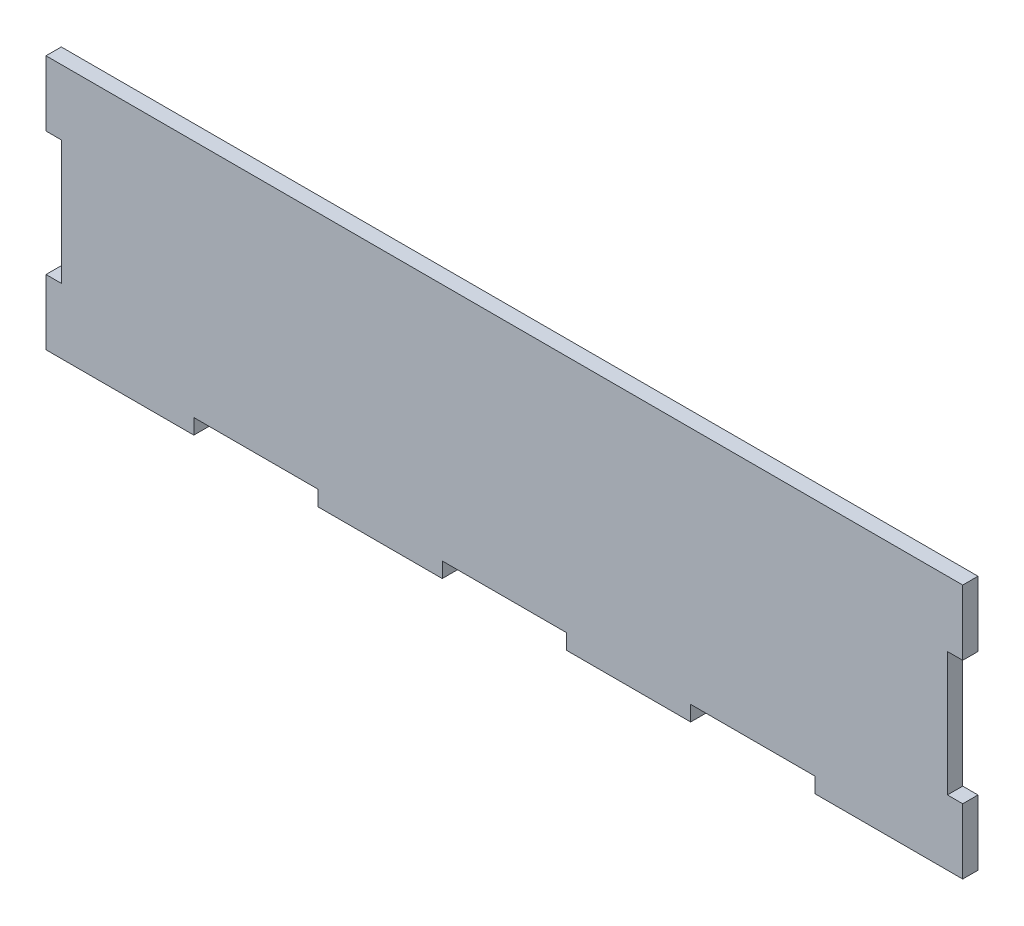
SolidWorks part; units mm, degrees
ref_plane "Alzado" through (0, 0, 0) normal (0, 0, 1) x (1, 0, 0)
ref_plane "Planta" through (0, 0, 0) normal (0, 1, 0) x (1, 0, 0)
ref_plane "Vista lateral" through (0, 0, 0) normal (1, 0, 0) x (0, 0, -1)
sketch "Model" plane through (0, 0, 0) normal (0, 0, 1) x (1, 0, 0)
  line L0 (0, 103) -> (0, 90.195)
  line L1 (0, 90.195) -> (3, 90.195)
  line L2 (3, 90.195) -> (3, 65.805)
  line L3 (3, 65.805) -> (0, 65.805)
  line L4 (0, 65.805) -> (0, 53)
  line L5 (0, 53) -> (29.025, 53)
  line L6 (29.025, 53) -> (29.025, 56)
  line L7 (29.025, 56) -> (53.415, 56)
  line L8 (53.415, 56) -> (53.415, 53)
  line L9 (53.415, 53) -> (77.805, 53)
  line L10 (77.805, 53) -> (77.805, 56)
  line L11 (77.805, 56) -> (102.195, 56)
  line L12 (102.195, 56) -> (102.195, 53)
  line L13 (102.195, 53) -> (126.585, 53)
  line L14 (126.585, 53) -> (126.585, 56)
  line L15 (126.585, 56) -> (150.975, 56)
  line L16 (150.975, 56) -> (150.975, 53)
  line L17 (150.975, 53) -> (175.365, 53)
  line L18 (175.365, 53) -> (180, 53)
  line L19 (180, 53) -> (180, 65.805)
  line L20 (180, 65.805) -> (177, 65.805)
  line L21 (177, 65.805) -> (177, 90.195)
  line L22 (177, 90.195) -> (180, 90.195)
  line L23 (180, 90.195) -> (180, 103)
  line L24 (180, 103) -> (0, 103)
extrude "Saliente-Extruir1" add sketch "Model" along normal blind 3
